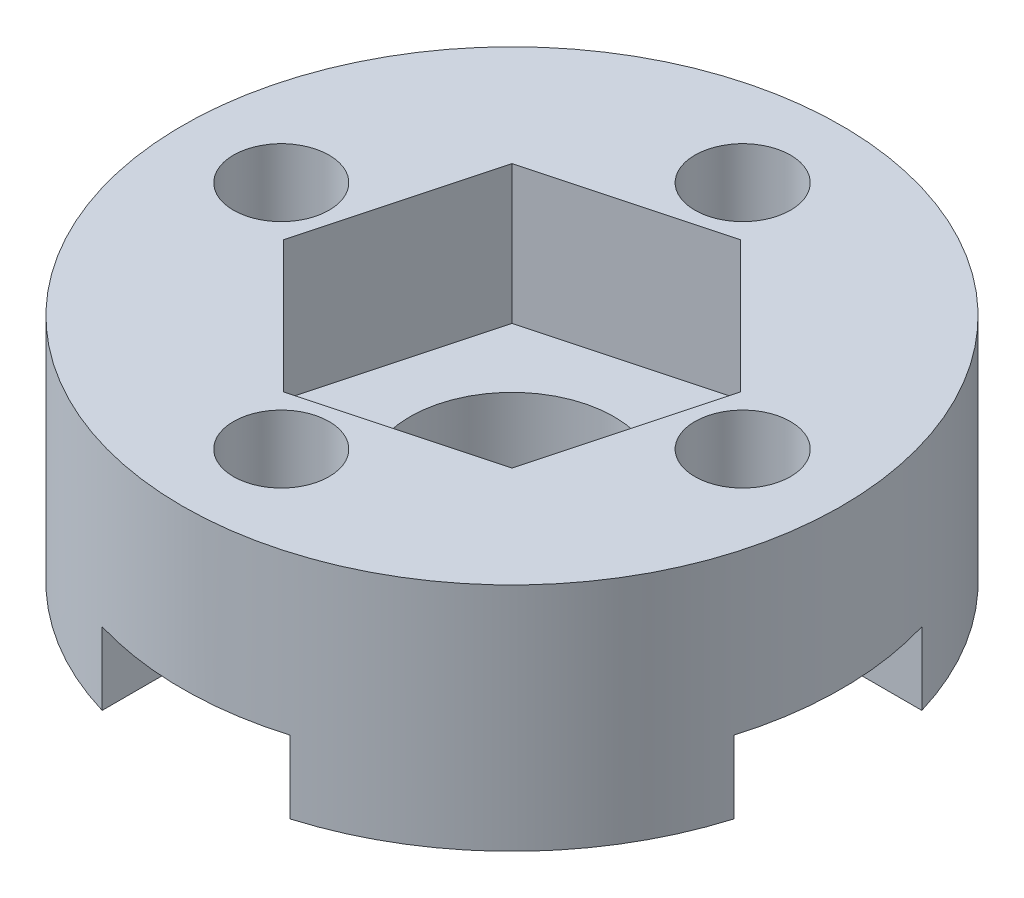
SolidWorks part; units mm, degrees
ref_plane "Front" through (0, 0, 0) normal (0, 0, 1) x (1, 0, 0)
ref_plane "Top" through (0, 0, 0) normal (0, 1, 0) x (1, 0, 0)
ref_plane "Right" through (0, 0, 0) normal (1, 0, 0) x (0, 0, -1)
sketch "Sketch1" plane through (0, 0, 0) normal (0, 1, 0) x (1, 0, 0)
  line L0 (0, 0) -> (0, 7) construction
  circle A0 centre (0, 0) radius 10
  circle A1 centre (0, 0) radius 3.1
  circle A2 centre (0, 7) radius 1.45
  circle A3 centre (7, 0) radius 1.45
  circle A4 centre (0, -7) radius 1.45
  circle A5 centre (-7, 0) radius 1.45
  point P14 (0, 0)
  dimension "D1" = 20
  dimension "D2" = 6.2
  dimension "D4" = 2.9
  dimension "D3" = 7
  dimension "D5" = 4
extrude "Boss-Extrude1" add sketch "Sketch1" along normal blind 7
sketch "Sketch8" plane through (0, 0, 0) normal (0, -1, 0) x (1, 0, 0)
  circle A0 centre (0, 0) radius 5.25
  circle A1 centre (0, 0) radius 3.1 construction
  circle A2 centre (0, 0) radius 3.1
  dimension "D1" = 10.5
extrude "Boss-Extrude4" add sketch "Sketch8" along normal blind 1 contours A0
sketch "Sketch9" plane through (0, -1, 0) normal (0, -1, 0) x (1, 0, 0)
  line L0 (-2.85, 7) -> (-2.85, 9.5853)
  line L1 (2.85, 7) -> (2.85, 9.5853)
  line L2 (7, -2.85) -> (9.5853, -2.85)
  line L3 (7, 2.85) -> (9.5853, 2.85)
  line L4 (-2.85, -7) -> (-2.85, -9.5853)
  line L5 (2.85, -7) -> (2.85, -9.5853)
  line L6 (-7, 2.85) -> (-9.5853, 2.85)
  line L7 (-7, -2.85) -> (-9.5853, -2.85)
  arc A0 (-2.85, 7) -> (2.85, 7) centre (0, 7) ccw
  circle A1 centre (0, 0) radius 10 construction
  circle A2 centre (0, 0) radius 10
  arc A3 (7, 2.85) -> (7, -2.85) centre (7, 0) ccw
  arc A4 (2.85, -7) -> (-2.85, -7) centre (0, -7) ccw
  arc A5 (-7, -2.85) -> (-7, 2.85) centre (-7, 0) ccw
  point P27 (0, 0)
  circle M5 centre (0, 0) radius 5.25
  dimension "D1" = 5.7
  dimension "D2" = 4
extrude "Cut-Extrude1" cut sketch "Sketch9" against normal blind 3.2 contours L7 A5 L6 A2 M5 | L1 A2 L0 A0 M5 | L3 A3 L2 A2 M5 | L5 A4 L4 A2 M5 | A5 M5 | A0 M5 | A3 M5 | A4 M5
hole_wizard "CSK for M3 Countersunk Flat Head Screw1" [suppressed] positions "3DSketch2" profile "Sketch6" countersink size "M3" standard "ISO"
sketch3d "3DSketch2"
  line L0 (0, 5.7, 7) -> (0, 0, 7) construction
  line L1 (7, 5.7, 0) -> (7, 0, 0) construction
  line L2 (0, 5.7, -7) -> (0, 0, -7) construction
  line L3 (-7, 5.7, 0) -> (-7, 0, 0) construction
  point P0 (0, 0, 7)
  point P4 (7, 0, 0)
  point P8 (0, 0, -7)
  point P12 (-7, 0, 0)
sketch "Sketch6" plane through (0, 0, 7) normal (1, 0, 0) x (0, 0, -1)
  line L0 (0, 0) -> (0, 5.7)
  line L1 (0, 5.7) -> (1.7, 5.7)
  line L2 (1.7, 5.7) -> (1.7, 1.2)
  line L3 (1.7, 1.2) -> (2.9, 0)
  line L5 (2.9, 0) -> (0, 0)
  line L6 (-1.7, 1.2) -> (-2.9, 0) construction
  line L11 (0, -6.35) -> (0, 107.95) construction
  dimension "Thru Hole Dia." = 3.4
  dimension "Thru Hole Depth" = 5.7
  dimension "Near C'Sink Dia." = 5.8
  dimension "Near C'Sink Angle" = 90
sketch "Sketch7" [suppressed] plane through (0, 0, 0) normal (0, -1, 0) x (1, 0, 0)
  circle A0 centre (0, 0) radius 5.5
  circle A1 centre (-7, 0) radius 2.9 construction
  circle A2 centre (0, -7) radius 2.9 construction
  circle A3 centre (7, 0) radius 2.9 construction
  circle A4 centre (0, 7) radius 2.9 construction
  circle A5 centre (-7, 0) radius 2.9
  circle A6 centre (0, -7) radius 2.9
  circle A7 centre (7, 0) radius 2.9
  circle A8 centre (0, 7) radius 2.9
  circle M2 centre (-7, 0) radius 2.9
  circle M4 centre (0, 0) radius 3.1
  circle M5 centre (0, -7) radius 2.9
  circle M6 centre (7, 0) radius 2.9
  circle M7 centre (0, 7) radius 2.9
  dimension "D1" = 11
extrude "Boss-Extrude3" [suppressed] add sketch "Sketch7" along normal blind 1 contours A0 M5 M6 M7 M2 M4
sketch "Sketch10" plane through (0, 7, 0) normal (0, 1, 0) x (1, 0, 0)
  line L0 (0, 0) -> (5.4652, 1.4644) construction
  line L1 (1.4644, 5.4652) -> (-4.0008, 4.0008)
  line L2 (-4.0008, 4.0008) -> (-5.4652, -1.4644)
  line L3 (-5.4652, -1.4644) -> (-1.4644, -5.4652)
  line L4 (-1.4644, -5.4652) -> (4.0008, -4.0008)
  line L5 (4.0008, -4.0008) -> (5.4652, 1.4644)
  line L6 (5.4652, 1.4644) -> (1.4644, 5.4652)
  line L7 (0, 0) -> (10, 0) construction
  circle A0 centre (0, 0) radius 4.9 construction
  circle A1 centre (0, 0) radius 10 construction
  dimension "D1" = 9.8
  dimension "D2" = 15
extrude "Cut-Extrude2" cut sketch "Sketch10" against normal blind 4.2
